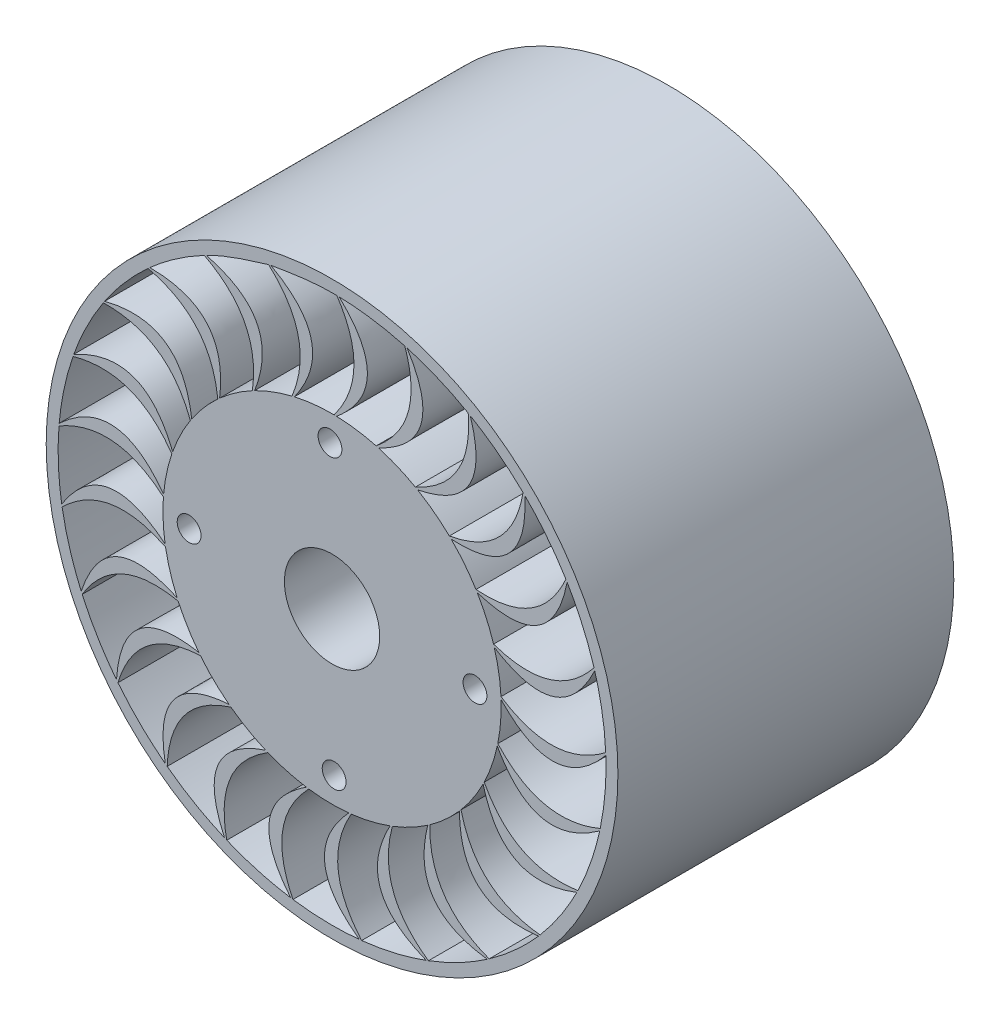
SolidWorks part; units mm, degrees
ref_plane "Front Plane" through (0, 0, 0) normal (0, 0, 1) x (1, 0, 0)
ref_plane "Top Plane" through (0, 0, 0) normal (0, 1, 0) x (1, 0, 0)
ref_plane "Right Plane" through (0, 0, 0) normal (1, 0, 0) x (0, 0, -1)
sketch "Sketch1" plane through (0, 0, 0) normal (0, 0, 1) x (1, 0, 0)
  circle A0 centre (0, 0) radius 50
  circle A1 centre (0, 0) radius 70
extrude "Boss-Extrude1" add sketch "Sketch1" along normal blind 30
sketch "Sketch2" plane through (0, 0, 30) normal (0, 0, 1) x (1, 0, 0)
  circle A0 centre (0, 0) radius 70
  circle A1 centre (0, 0) radius 34
extrude "Boss-Extrude2" add sketch "Sketch2" along normal blind 81
sketch "Sketch3" plane through (0, 0, 111) normal (0, 0, 1) x (1, 0, 0)
  circle A0 centre (0, 0) radius 20
  circle A1 centre (0, 0) radius 70
  dimension "D1" = 40
extrude "Boss-Extrude3" add sketch "Sketch3" along normal blind 30
sketch "Sketch5" plane through (0, 0, 141) normal (0, 0, 1) x (1, 0, 0)
  circle A1 centre (0, 0) radius 70
  circle A3 centre (0, 0) radius 120
  spline S0 degree 2 poles (3.0104, 114.9606) (27.186, 92.132) (1.8805, 70.9751) knots 0 0 0 1 1 1
  spline S1 degree 2 poles (2.0106, 114.9846) (16.923, 92.4705) (0.8808, 70.9981) knots 0 0 0 1 1 1
  spline S2 degree 2 poles (30.543, 110.8721) (39.3878, 85.3568) (18.5096, 68.5485) knots 0 0 0 1 1 1
  spline S3 degree 2 poles (31.5053, 110.6002) (49.2442, 82.4766) (19.4722, 68.2776) knots 0 0 0 1 1 1
  spline S4 degree 2 poles (57.1562, 99.7931) (59.3777, 72.8798) (34.9754, 61.7918) knots 0 0 0 1 1 1
  spline S5 degree 2 poles (58.0207, 99.2905) (68.2083, 67.6389) (35.8404, 61.29) knots 0 0 0 1 1 1
  spline S6 degree 2 poles (80.1781, 82.4438) (75.6367, 55.8235) (49.2436, 51.1524) knots 0 0 0 1 1 1
  spline S7 degree 2 poles (80.8904, 81.7419) (82.8865, 48.5512) (49.9566, 50.4513) knots 0 0 0 1 1 1
  spline S8 degree 2 poles (98.1621, 59.9142) (87.1432, 35.2596) (60.4176, 37.299) knots 0 0 0 1 1 1
  spline S9 degree 2 poles (98.6775, 59.0572) (92.3567, 26.4129) (60.9339, 36.4426) knots 0 0 0 1 1 1
  spline S10 degree 2 poles (109.9782, 33.62) (93.1742, 12.4802) (67.7953, 21.102) knots 0 0 0 1 1 1
  spline S11 degree 2 poles (110.2643, 32.6618) (96.0237, 2.6149) (68.0824, 20.1441) knots 0 0 0 1 1 1
  spline S12 degree 2 poles (114.8839, 5.2133) (93.3506, -11.0833) (70.9133, 3.579) knots 0 0 0 1 1 1
  spline S13 degree 2 poles (114.9228, 4.214) (93.6573, -21.3474) (70.9531, 2.5798) knots 0 0 0 1 1 1
  spline S14 degree 2 poles (112.5711, -23.521) (87.6615, -33.9505) (69.5755, -14.1689) knots 0 0 0 1 1 1
  spline S15 degree 2 poles (112.3602, -24.4985) (85.406, -43.9683) (69.3656, -15.1466) knots 0 0 0 1 1 1
  spline S16 degree 2 poles (103.1851, -50.7773) (76.4644, -54.6844) (63.866, -31.0264) knots 0 0 0 1 1 1
  spline S17 degree 2 poles (102.7377, -51.6717) (71.7883, -63.8266) (63.4195, -31.9212) knots 0 0 0 1 1 1
  spline S18 degree 2 poles (87.3155, -74.8432) (60.4626, -71.9823) (54.1435, -45.9345) knots 0 0 0 1 1 1
  spline S19 degree 2 poles (86.6598, -75.5982) (53.6599, -79.6744) (53.4886, -46.6902) knots 0 0 0 1 1 1
  spline S20 degree 2 poles (65.9596, -94.2063) (40.6618, -84.7573) (41.0191, -57.9563) knots 0 0 0 1 1 1
  spline S21 degree 2 poles (65.1367, -94.7745) (32.1599, -90.5159) (40.1968, -58.5254) knots 0 0 0 1 1 1
  spline S22 degree 2 poles (40.4592, -107.6501) (18.3061, -92.2067) (25.3172, -66.3366) knots 0 0 0 1 1 1
  spline S23 degree 2 poles (39.5209, -107.9958) (8.6391, -95.67) (24.3792, -66.6832) knots 0 0 0 1 1 1
  spline S24 degree 2 poles (12.4166, -114.3299) (-5.1999, -93.8624) (8.0246, -70.5486) knots 0 0 0 1 1 1
  spline S25 degree 2 poles (11.4218, -114.4314) (-15.4245, -94.8129) (7.0299, -70.6511) knots 0 0 0 1 1 1
  spline S26 degree 2 poles (-16.4062, -113.8259) (-28.3792, -89.6203) (-9.7722, -70.3278) knots 0 0 0 1 1 1
  spline S27 degree 2 poles (-17.395, -113.6768) (-38.5189, -87.9982) (-10.7612, -70.1797) knots 0 0 0 1 1 1
  spline S28 degree 2 poles (-44.1981, -106.1698) (-49.7753, -79.7471) (-26.955, -65.6881) knots 0 0 0 1 1 1
  spline S29 degree 2 poles (-45.1188, -105.7795) (-59.193, -75.6543) (-27.8761, -65.2987) knots 0 0 0 1 1 1
  spline S30 degree 2 poles (-69.2129, -91.8427) (-68.0438, -64.8631) (-42.4442, -56.9209) knots 0 0 0 1 1 1
  spline S31 degree 2 poles (-70.0076, -91.2356) (-76.1478, -58.5568) (-43.2395, -56.3147) knots 0 0 0 1 1 1
  spline S32 degree 2 poles (-89.8788, -71.7447) (-82.0369, -45.9035) (-55.2664, -44.5772) knots 0 0 0 1 1 1
  spline S33 degree 2 poles (-90.4975, -70.9591) (-88.318, -37.78) (-55.8859, -43.7923) knots 0 0 0 1 1 1
  spline S34 degree 2 poles (-104.8973, -47.1388) (-90.8753, -24.0596) (-64.616, -29.4326) knots 0 0 0 1 1 1
  spline S35 degree 2 poles (-105.3012, -46.224) (-94.9388, -14.6292) (-65.0209, -28.5182) knots 0 0 0 1 1 1
  spline S36 degree 2 poles (-113.3247, -19.5709) (-94.0036, -0.704) (-69.9055, -12.4386) knots 0 0 0 1 1 1
  spline S37 degree 2 poles (-113.4884, -18.5844) (-95.5943, 9.4407) (-70.0703, -11.4522) knots 0 0 0 1 1 1
  spline S38 degree 2 poles (-114.6315, 9.2266) (-91.2254, 22.6959) (-70.8027, 5.337) knots 0 0 0 1 1 1
  spline S39 degree 2 poles (-114.5447, 10.2229) (-90.2432, 32.9174) (-70.717, 6.3333) knots 0 0 0 1 1 1
  spline S40 degree 2 poles (-108.7355, 37.4444) (-82.7152, 44.6697) (-67.251, 22.7772) knots 0 0 0 1 1 1
  spline S41 degree 2 poles (-108.4038, 38.3878) (-79.2218, 54.3258) (-66.9202, 23.721) knots 0 0 0 1 1 1
  spline S42 degree 2 poles (-96.0073, 63.3095) (-69.0076, 63.8367) (-59.4737, 38.7863) knots 0 0 0 1 1 1
  spline S43 degree 2 poles (-95.4514, 64.1407) (-63.2226, 72.3207) (-58.9186, 39.6181) knots 0 0 0 1 1 1
  spline S44 degree 2 poles (-77.2467, 85.1965) (-50.9641, 78.9927) (-47.9595, 52.3583) knots 0 0 0 1 1 1
  spline S45 degree 2 poles (-76.5015, 85.8634) (-43.2509, 85.7715) (-47.215, 53.0259) knots 0 0 0 1 1 1
  spline S46 degree 2 poles (-53.6323, 101.7304) (-29.7183, 89.1852) (-33.4318, 62.6404) knots 0 0 0 1 1 1
  spline S47 degree 2 poles (-52.7447, 102.191) (-20.5616, 93.8329) (-32.5446, 63.1019) knots 0 0 0 1 1 1
  spline S48 degree 2 poles (-26.648, 111.8722) (-6.6052, 93.7739) (-16.8034, 68.9866) knots 0 0 0 1 1 1
  spline S49 degree 2 poles (-25.6738, 112.0975) (3.4196, 95.9984) (-15.8294, 69.2129) knots 0 0 0 1 1 1
  spline S50 degree 3 poles (-25.6738, 112.0975) (-16.4683, 113.6257) (-7.2628, 115.1539) (2.0106, 114.9846) knots 0 0 0 0 0.038666 0.038666 0.038666 0.038666
  spline S51 degree 3 poles (-52.7447, 102.191) (-44.4873, 106.4156) (-35.5677, 109.1439) (-26.648, 111.8722) knots 0.961334 0.961334 0.961334 0.961334 1 1 1 1
  spline S52 degree 3 poles (-76.5015, 85.8634) (-69.5599, 92.0211) (-61.8478, 97.4134) (-53.6323, 101.7304) knots 0.921278 0.921278 0.921278 0.921278 0.959944 0.959944 0.959944 0.959944
  spline S53 degree 3 poles (-95.4514, 64.1407) (-90.2593, 71.8314) (-84.1332, 78.978) (-77.2467, 85.1965) knots 0.881222 0.881222 0.881222 0.881222 0.919889 0.919889 0.919889 0.919889
  spline S54 degree 3 poles (-108.4038, 38.3878) (-105.2874, 47.1281) (-101.1311, 55.5737) (-96.0073, 63.3095) knots 0.841167 0.841167 0.841167 0.841167 0.879833 0.879833 0.879833 0.879833
  spline S55 degree 3 poles (-114.5447, 10.2229) (-113.6999, 19.4636) (-111.7745, 28.6775) (-108.7355, 37.4444) knots 0.801111 0.801111 0.801111 0.801111 0.839778 0.839778 0.839778 0.839778
  spline S56 degree 3 poles (-113.4884, -18.5844) (-114.9682, -9.4239) (-115.3947, -0.0207) (-114.6315, 9.2266) knots 0.761056 0.761056 0.761056 0.761056 0.799722 0.799722 0.799722 0.799722
  spline S57 degree 3 poles (-105.3012, -46.224) (-109.0126, -37.7193) (-111.7642, -28.7175) (-113.3247, -19.5709) knots 0.721 0.721 0.721 0.721 0.759667 0.759667 0.759667 0.759667
  spline S58 degree 3 poles (-90.4975, -70.9591) (-96.2074, -63.6446) (-101.1112, -55.6099) (-104.8973, -47.1388) knots 0.680945 0.680945 0.680945 0.680945 0.719611 0.719611 0.719611 0.719611
  spline S59 degree 3 poles (-70.0076, -91.2356) (-77.3571, -85.5709) (-84.105, -79.0082) (-89.8788, -71.7447) knots 0.640889 0.640889 0.640889 0.640889 0.679555 0.679555 0.679555 0.679555
  spline S60 degree 3 poles (-45.1188, -105.7795) (-53.6461, -102.1205) (-61.8141, -97.442) (-69.2129, -91.8427) knots 0.600833 0.600833 0.600833 0.600833 0.6395 0.6395 0.6395 0.6395
  spline S61 degree 3 poles (-17.395, -113.6768) (-26.5644, -112.2534) (-35.6393, -109.7533) (-44.1981, -106.1698) knots 0.560778 0.560778 0.560778 0.560778 0.599444 0.599444 0.599444 0.599444
  spline S62 degree 3 poles (11.4218, -114.4314) (2.1864, -115.3331) (-7.2251, -115.1683) (-16.4062, -113.8259) knots 0.520722 0.520722 0.520722 0.520722 0.559389 0.559389 0.559389 0.559389
  spline S63 degree 3 poles (39.5209, -107.9958) (30.7999, -111.1659) (21.6431, -113.3469) (12.4166, -114.3299) knots 0.480667 0.480667 0.480667 0.480667 0.519333 0.519333 0.519333 0.519333
  spline S64 degree 3 poles (65.1367, -94.7745) (57.4781, -100.0138) (49.1514, -104.4035) (40.4592, -107.6501) knots 0.440611 0.440611 0.440611 0.440611 0.479278 0.479278 0.479278 0.479278
  spline S65 degree 3 poles (86.6598, -75.5982) (80.5448, -82.5775) (73.5713, -88.9) (65.9596, -94.2063) knots 0.400556 0.400556 0.400556 0.400556 0.439222 0.439222 0.439222 0.439222
  spline S66 degree 3 poles (102.7377, -51.6717) (98.5505, -59.9525) (93.3684, -67.8106) (87.3155, -74.8432) knots 0.3605 0.3605 0.3605 0.3605 0.399167 0.399167 0.399167 0.399167
  spline S67 degree 3 poles (112.3602, -24.4985) (110.3639, -33.5605) (107.2989, -42.4604) (103.1851, -50.7773) knots 0.320445 0.320445 0.320445 0.320445 0.359111 0.359111 0.359111 0.359111
  spline S68 degree 3 poles (114.9228, 4.214) (115.2428, -5.0597) (114.4874, -14.4423) (112.5711, -23.521) knots 0.280389 0.280389 0.280389 0.280389 0.319055 0.319055 0.319055 0.319055
  spline S69 degree 3 poles (110.2643, 32.6618) (112.8805, 23.759) (114.4822, 14.4833) (114.8839, 5.2133) knots 0.240333 0.240333 0.240333 0.240333 0.279 0.279 0.279 0.279
  spline S70 degree 3 poles (98.6775, 59.0572) (103.4255, 51.0848) (107.2837, 42.4988) (109.9782, 33.62) knots 0.200278 0.200278 0.200278 0.200278 0.238944 0.238944 0.238944 0.238944
  spline S71 degree 3 poles (80.8904, 81.7419) (87.472, 75.2007) (93.3441, 67.844) (98.1621, 59.9142) knots 0.160222 0.160222 0.160222 0.160222 0.198889 0.198889 0.198889 0.198889
  spline S72 degree 3 poles (58.0207, 99.2905) (66.0222, 94.5916) (73.5394, 88.9263) (80.1781, 82.4438) knots 0.120167 0.120167 0.120167 0.120167 0.158833 0.158833 0.158833 0.158833
  spline S73 degree 3 poles (31.5053, 110.6002) (40.4241, 108.0388) (49.114, 104.421) (57.1562, 99.7931) knots 0.080111 0.080111 0.080111 0.080111 0.118778 0.118778 0.118778 0.118778
  spline S74 degree 3 poles (3.0104, 114.9606) (12.2876, 114.692) (21.6026, 113.3545) (30.543, 110.8721) knots 0.040056 0.040056 0.040056 0.040056 0.078722 0.078722 0.078722 0.078722
  spline S75 degree 2 poles (-15.8294, 69.2129) (-7.5176, 71.1352) (0.8808, 70.9981) knots 0 0 0 0.037884 0.037884 0.037884
  spline S76 degree 2 poles (-32.5446, 63.1019) (-25.0627, 66.9219) (-16.8034, 68.9866) knots 0.962116 0.962116 0.962116 1 1 1
  spline S77 degree 3 poles (-47.215, 53.0259) (-43.0178, 56.7375) (-38.3827, 60.0164) (-33.4318, 62.6404) knots 0.921978 0.921978 0.921978 0.921978 0.959862 0.959862 0.959862 0.959862
  spline S78 degree 3 poles (-58.9186, 39.6181) (-55.7764, 44.257) (-52.1026, 48.5876) (-47.9595, 52.3583) knots 0.88184 0.88184 0.88184 0.88184 0.919724 0.919724 0.919724 0.919724
  spline S79 degree 3 poles (-66.9202, 23.721) (-65.0303, 28.9955) (-62.549, 34.1038) (-59.4737, 38.7863) knots 0.841702 0.841702 0.841702 0.841702 0.879586 0.879586 0.879586 0.879586
  spline S80 degree 3 poles (-70.717, 6.3333) (-70.1982, 11.9122) (-69.0652, 17.477) (-67.251, 22.7772) knots 0.801564 0.801564 0.801564 0.801564 0.839448 0.839448 0.839448 0.839448
  spline S81 degree 3 poles (-70.0703, -11.4522) (-70.9552, -5.9196) (-71.2417, -0.2478) (-70.8027, 5.337) knots 0.761426 0.761426 0.761426 0.761426 0.79931 0.79931 0.79931 0.79931
  spline S82 degree 3 poles (-65.0209, -28.5182) (-67.2536, -23.3801) (-68.9419, -17.9572) (-69.9055, -12.4386) knots 0.721289 0.721289 0.721289 0.721289 0.759172 0.759172 0.759172 0.759172
  spline S83 degree 2 poles (-64.616, -29.4326) (-61.0455, -37.16) (-55.8859, -43.7923) knots 0 0 0 0.485553 0.485553 0.485553
  spline S84 degree 2 poles (-55.2664, -44.5772) (-50.0142, -51.1359) (-43.2395, -56.3147) knots 0.514447 0.514447 0.514447 1 1 1
  spline S85 degree 3 poles (-27.8761, -65.2987) (-33.0216, -63.0813) (-37.9638, -60.2829) (-42.4442, -56.9209) knots 0.601472 0.601472 0.601472 0.601472 0.639356 0.639356 0.639356 0.639356
  spline S86 degree 3 poles (-10.7612, -70.1797) (-16.2965, -69.3117) (-21.7792, -67.8315) (-26.955, -65.6881) knots 0.561334 0.561334 0.561334 0.561334 0.599218 0.599218 0.599218 0.599218
  spline S87 degree 3 poles (7.0299, -70.6511) (1.4526, -71.1869) (-4.226, -71.1167) (-9.7722, -70.3278) knots 0.521196 0.521196 0.521196 0.521196 0.55908 0.55908 0.55908 0.55908
  spline S88 degree 3 poles (24.3792, -66.6832) (19.1105, -68.5892) (13.5928, -69.9334) (8.0246, -70.5486) knots 0.481058 0.481058 0.481058 0.481058 0.518942 0.518942 0.518942 0.518942
  spline S89 degree 3 poles (40.1968, -58.5254) (35.5675, -61.6817) (30.5575, -64.3559) (25.3172, -66.3366) knots 0.44092 0.44092 0.44092 0.44092 0.478804 0.478804 0.478804 0.478804
  spline S90 degree 3 poles (53.4886, -46.6902) (49.7897, -50.8986) (45.6021, -54.7347) (41.0191, -57.9563) knots 0.400782 0.400782 0.400782 0.400782 0.438666 0.438666 0.438666 0.438666
  spline S91 degree 3 poles (63.4195, -31.9212) (60.8834, -36.9173) (57.7814, -41.6743) (54.1435, -45.9345) knots 0.360644 0.360644 0.360644 0.360644 0.398528 0.398528 0.398528 0.398528
  spline S92 degree 3 poles (69.3656, -15.1466) (68.1516, -20.6164) (66.3301, -25.9954) (63.866, -31.0264) knots 0.320506 0.320506 0.320506 0.320506 0.35839 0.35839 0.35839 0.35839
  spline S93 degree 3 poles (70.9531, 2.5798) (71.1376, -3.0201) (70.711, -8.6831) (69.5755, -14.1689) knots 0.280368 0.280368 0.280368 0.280368 0.318252 0.318252 0.318252 0.318252
  spline S94 degree 3 poles (68.0824, 20.1441) (69.6538, 14.766) (70.6489, 9.1748) (70.9133, 3.579) knots 0.24023 0.24023 0.24023 0.24023 0.278114 0.278114 0.278114 0.278114
  spline S95 degree 3 poles (60.9339, 36.4426) (63.7933, 31.6243) (66.1476, 26.4563) (67.7953, 21.102) knots 0.200092 0.200092 0.200092 0.200092 0.237976 0.237976 0.237976 0.237976
  spline S96 degree 3 poles (49.9566, 50.4513) (53.924, 46.496) (57.4901, 42.0754) (60.4176, 37.299) knots 0.159954 0.159954 0.159954 0.159954 0.197838 0.197838 0.197838 0.197838
  spline S97 degree 3 poles (19.4722, 68.2776) (24.8569, 66.7244) (30.109, 64.567) (34.9754, 61.7918) knots 0.027315 0.027315 0.027315 0.027315 0.486343 0.486343 0.486343 0.486343
  spline S98 degree 3 poles (35.8404, 61.29) (40.6673, 58.4452) (45.2177, 55.05) (49.2436, 51.1524) knots 0.513657 0.513657 0.513657 0.513657 0.972685 0.972685 0.972685 0.972685
  spline S99 degree 3 poles (1.8805, 70.9751) (7.4821, 70.8094) (13.1063, 70.0251) (18.5096, 68.5485) knots 0.040138 0.040138 0.040138 0.040138 0.078022 0.078022 0.078022 0.078022
  point P156 (0, 0)
  point P157 (0, 0)
extrude "Boss-Extrude4" add sketch "Sketch5" against normal blind 141
sketch "Sketch6" plane through (0, 0, 0) normal (0, 0, -1) x (-1, 0, 0)
  circle A0 centre (0.8678, 60) radius 5
  circle A1 centre (60, -0.8678) radius 5
  circle A2 centre (-0.8678, -60) radius 5
  circle A3 centre (-60, 0.8678) radius 5
  point P13 (0, 0)
  dimension "D1" = 4
  dimension "D2" = 60
extrude "Cut-Extrude1" cut sketch "Sketch6" against normal through all
